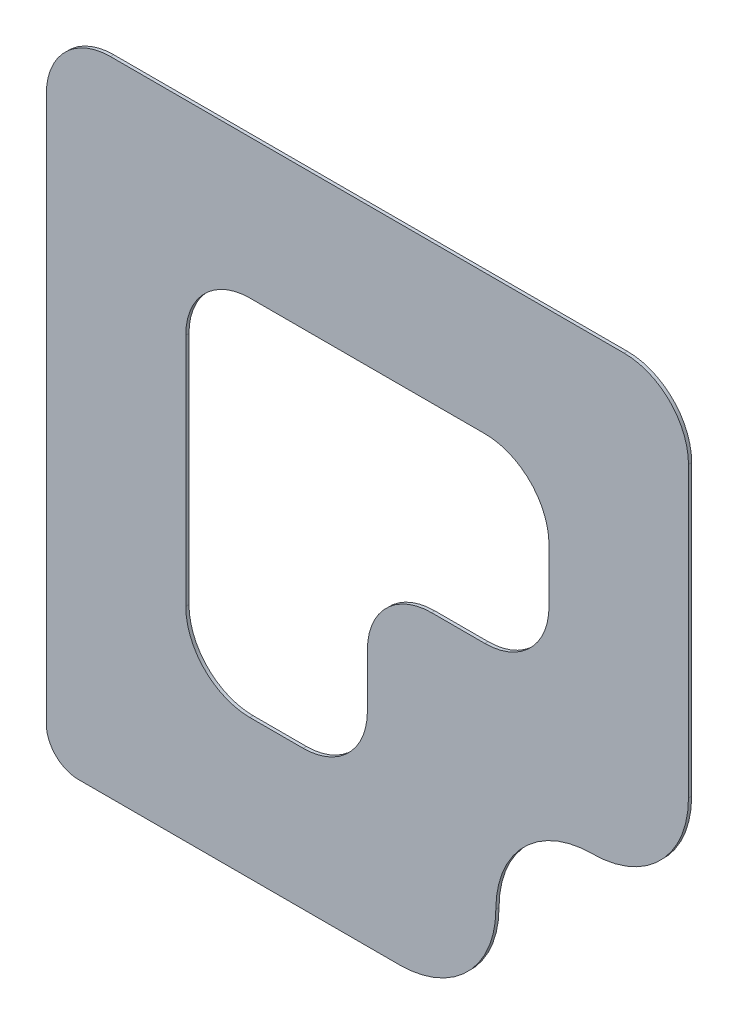
SolidWorks part; units mm, degrees
ref_plane "Alzado" through (0, 0, 0) normal (0, 0, 1) x (1, 0, 0)
ref_plane "Planta" through (0, 0, 0) normal (0, 1, 0) x (1, 0, 0)
ref_plane "Vista lateral" through (0, 0, 0) normal (1, 0, 0) x (0, 0, -1)
sketch "Model" plane through (0, 0, 0) normal (0, 0, 1) x (1, 0, 0)
  line L0 (20.5, 22) -> (28.5, 22)
  line L1 (19.5, 40) -> (19.5, 23)
  line L2 (37.5, 42) -> (21.5, 42)
  line L3 (39.5, 33) -> (39.5, 40)
  line L4 (31.5, 32) -> (33.1569, 32)
  line L5 (29.5, 30) -> (29.5, 28.3431)
  line L6 (23.8431, 35.6569) -> (23.8431, 28.3431)
  line L7 (25.8431, 26.3431) -> (27.5, 26.3431)
  line L8 (35.1569, 34) -> (35.1569, 35.6569)
  line L9 (33.1569, 37.6569) -> (25.8431, 37.6569)
  line L10 (30.5, 22) -> (28.5, 22)
  line L11 (39.5, 31) -> (39.5, 33)
  arc A0 (19.5, 23) -> (20.5, 22) centre (20.5, 23) ccw
  arc A1 (21.5, 42) -> (19.5, 40) centre (21.5, 40) ccw
  arc A2 (39.5, 40) -> (37.5, 42) centre (37.5, 40) ccw
  arc A3 (25.8431, 37.6569) -> (23.8431, 35.6569) centre (25.8431, 35.6569) ccw
  arc A4 (35.1569, 35.6569) -> (33.1569, 37.6569) centre (33.1569, 35.6569) ccw
  arc A5 (23.8431, 28.3431) -> (25.8431, 26.3431) centre (25.8431, 28.3431) ccw
  arc A6 (31.5, 32) -> (29.5, 30) centre (31.5, 30) ccw
  arc A7 (27.5, 26.3431) -> (29.5, 28.3431) centre (27.5, 28.3431) ccw
  arc A8 (33.1569, 32) -> (35.1569, 34) centre (33.1569, 34) ccw
  arc A9 (30.5, 22) -> (33.5, 25) centre (30.5, 25) ccw
  arc A10 (36.5, 28) -> (33.5, 25) centre (36.5, 25) ccw
  arc A11 (36.5, 28) -> (39.5, 31) centre (36.5, 31) ccw
extrude "Saliente-Extruir1" add sketch "Model" along normal blind 0.1
